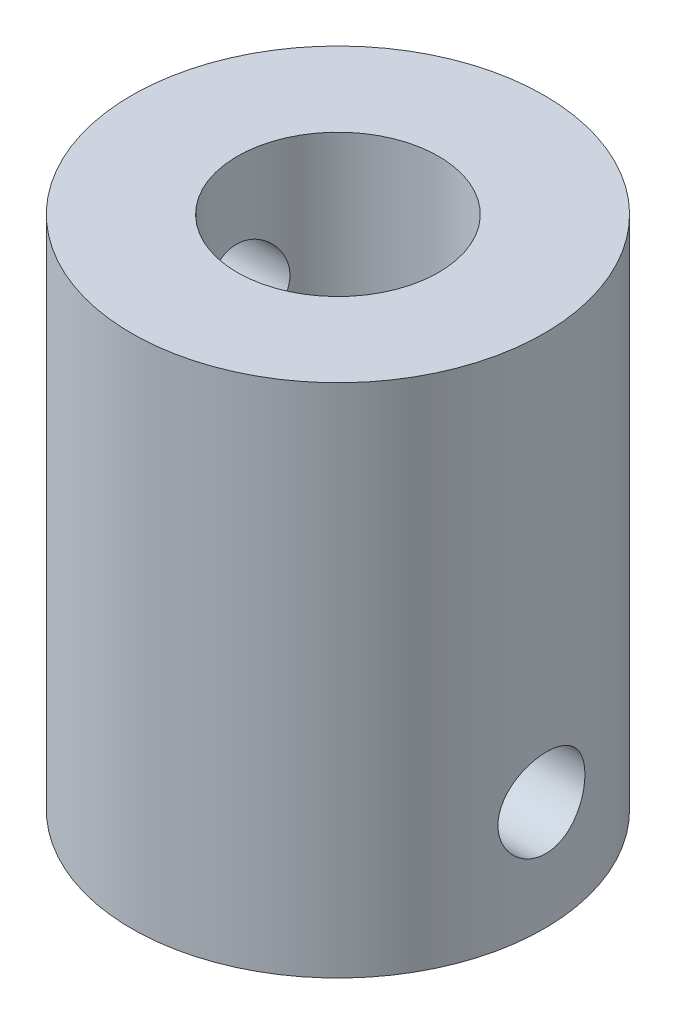
SolidWorks part; units mm, degrees
ref_plane "Front Plane" through (0, 0, 0) normal (0, 0, 1) x (1, 0, 0)
ref_plane "Top Plane" through (0, 0, 0) normal (0, 1, 0) x (1, 0, 0)
ref_plane "Right Plane" through (0, 0, 0) normal (1, 0, 0) x (0, 0, -1)
sketch "Sketch1" plane through (0, 0, 0) normal (0, -1, 0) x (0, 0, -1)
  circle A0 centre (0, 0) radius 6.35
  dimension "D1" = 12.7
extrude "Boss-Extrude1" add sketch "Sketch1" along normal blind 15.875
sketch "Sketch2" plane through (0, 0, 0) normal (0, 1, 0) x (1, 0, 0)
  circle A0 centre (0, 0) radius 3.1
  dimension "D1" = 6.2
extrude "Cut-Extrude1" cut sketch "Sketch2" against normal blind 9.525
sketch "Sketch3" plane through (0, -15.875, 0) normal (0, -1, 0) x (1, 0, 0)
  circle A0 centre (0, 0) radius 4.1
  dimension "D1" = 8.2
extrude "Cut-Extrude2" cut sketch "Sketch3" against normal up to surface (6.35 mm away) up to face at (0, -9.525, 3.1)
sketch "Sketch11" plane through (0, 0, 0) normal (1, 0, 0) x (0, 0, -1)
  line L0 (0, 0) -> (0, -14.8732) construction
hole_wizard "#6-32 Tapped Hole1" positions "3DSketch5" profile "Sketch12" tap size "#6-32" standard "ANSI Inch"
sketch3d "3DSketch5"
  line L0 (0, 0, 0) -> (0, -14.8732, 0) construction
  point P0 (0, -5, 0)
  point P7 (0, -2.9681, 0)
  point P9 (-6.3497, -3.6851, 0.0615)
  dimension "D1" = 5
sketch "Sketch12" plane through (-6.3497, -3.6851, 0.0615) normal (0, 1, 0) x (0.0097, 0, 1)
  line L0 (0, 0) -> (0, 7.8127)
  line L1 (0, 7.8127) -> (1.3525, 7)
  line L2 (1.3525, 7) -> (1.3525, 0)
  line L5 (1.3525, 0) -> (0, 0)
  line L10 (0, 7.8127) -> (-1.3526, 7) construction
  line L11 (0, -6.35) -> (0, 107.95) construction
  dimension "Tap Drill Dia." = 2.7051
  dimension "Tap Drill Depth" = 7
  dimension "Drill Angle" = 118
cosmetic thread "Hole Thread6" parameters "D1"=3.5606, "D2"=3.5052
hole_wizard "#6-32 Tapped Hole2" positions "3DSketch6" profile "Sketch13" tap size "#6-32" standard "ANSI Inch" end condition through all
sketch3d "3DSketch6"
  point P0 (-6.3497, -12.5453, 0.0629)
sketch "Sketch13" plane through (-6.3497, -12.5453, 0.0629) normal (0, 1, 0) x (0.0099, 0, 1)
  line L0 (0, 0) -> (0, 12.7626)
  line L1 (0, 12.7626) -> (1.3525, 12.7626)
  line L2 (1.3525, 12.7626) -> (1.3525, 0)
  line L5 (1.3525, 0) -> (0, 0)
  line L11 (0, -6.35) -> (0, 107.95) construction
  dimension "Thru Tap Drill Dia." = 2.7051
  dimension "Thru Tap Drill Depth" = 12.7626
cosmetic thread "Hole Thread7"
